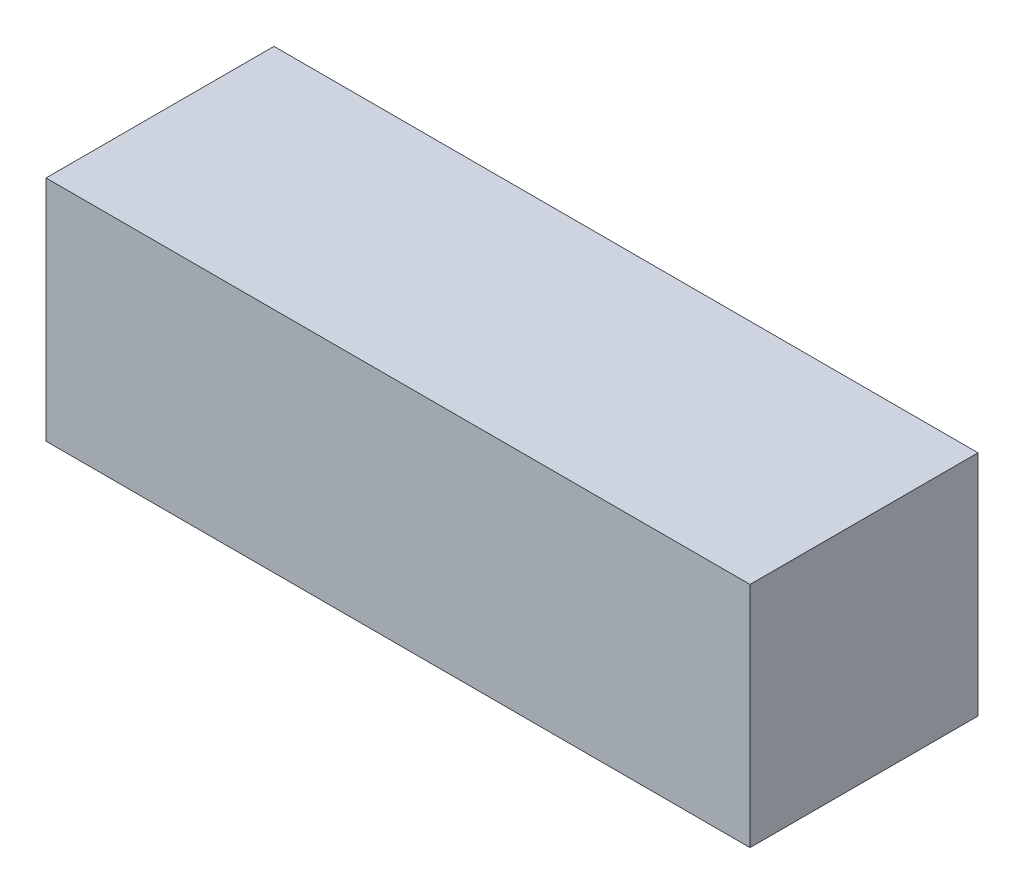
SolidWorks part; units mm, degrees
ref_plane "Front Plane" through (0, 0, 0) normal (0, 0, 1) x (1, 0, 0)
ref_plane "Top Plane" through (0, 0, 0) normal (0, 1, 0) x (1, 0, 0)
ref_plane "Right Plane" through (0, 0, 0) normal (1, 0, 0) x (0, 0, -1)
other "Bounding Box"
ref_plane "Default Plane" through (13.8565, 3.175, 6.7999) normal (0, -1, 0) x (-1, 0, 0)
sketch "Sketch1" plane through (0, 0, 0) normal (0, 1, 0) x (1, 0, 0)
  line L1 (-26.67, -8.636) -> (26.67, -8.636)
  line L2 (-26.67, -8.636) -> (-26.67, 8.636)
  line L3 (-26.67, 8.636) -> (26.67, 8.636)
  line L4 (26.67, -8.636) -> (26.67, 8.636)
  line L5 (-26.67, -8.636) -> (26.67, 8.636) construction
  line L6 (-26.67, 8.636) -> (26.67, -8.636) construction
  point P0 (0, 0)
  dimension "D1" = 17.272
  dimension "D2" = 53.34
extrude "Boss-Extrude1" add sketch "Sketch1" along normal mid plane 17.272
